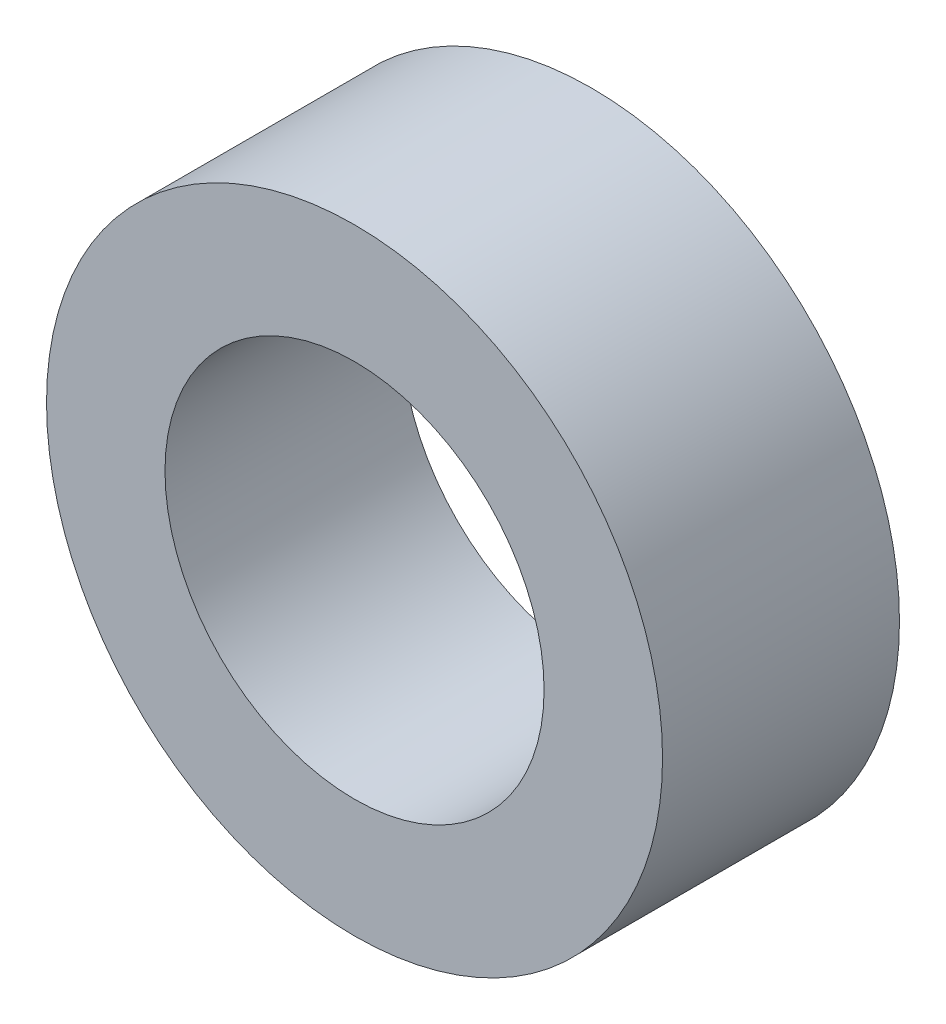
SolidWorks part; units mm, degrees
ref_plane "Front Plane" through (0, 0, 0) normal (0, 0, 1) x (1, 0, 0)
ref_plane "Top Plane" through (0, 0, 0) normal (0, 1, 0) x (1, 0, 0)
ref_plane "Right Plane" through (0, 0, 0) normal (1, 0, 0) x (0, 0, -1)
sketch "Sketch1" plane through (0, 0, 0) normal (0, 0, 1) x (1, 0, 0)
  circle A0 centre (0, 0) radius 4
  circle A1 centre (0, 0) radius 6.5
  dimension "D1" = 13
  dimension "D2" = 8
extrude "Boss-Extrude1" add sketch "Sketch1" along normal blind 5
